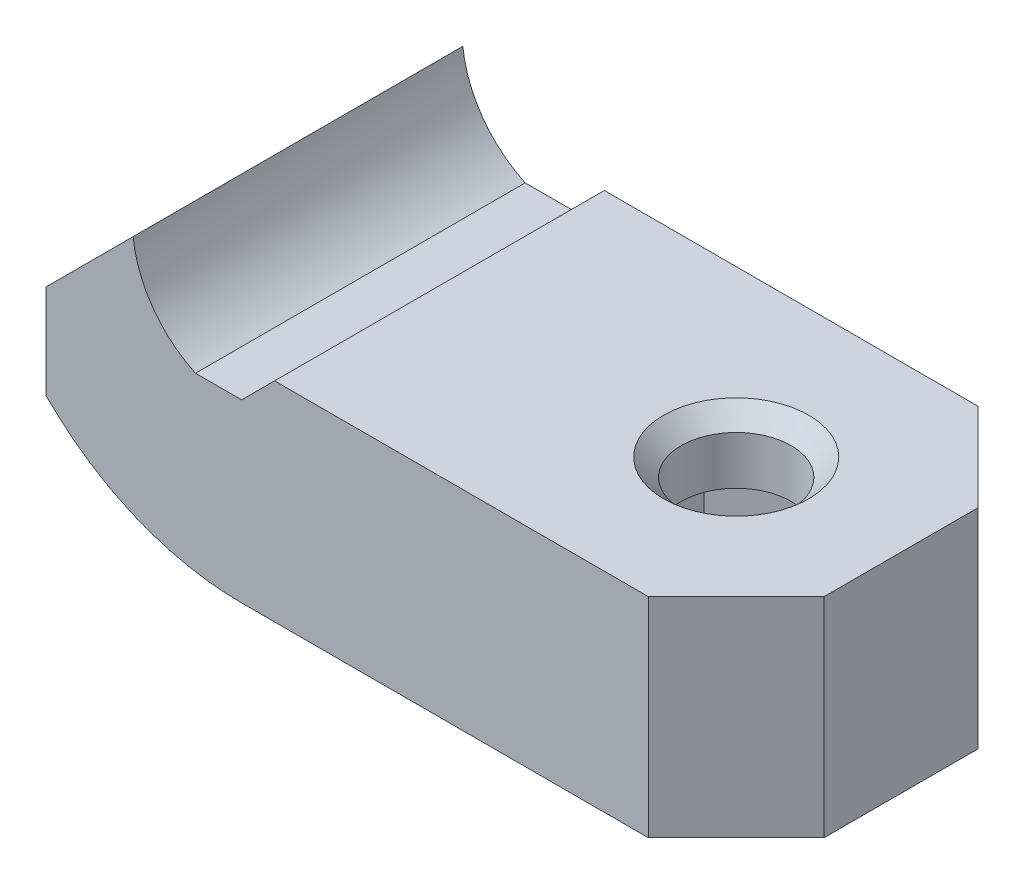
SolidWorks part; units mm, degrees
ref_plane "Alzado" through (0, 0, 0) normal (0, 0, 1) x (1, 0, 0)
ref_plane "Planta" through (0, 0, 0) normal (0, 1, 0) x (1, 0, 0)
ref_plane "Vista lateral" through (0, 0, 0) normal (1, 0, 0) x (0, 0, -1)
sketch "Croquis1" plane through (0, 0, 0) normal (0, 0, 1) x (1, 0, 0)
  line L0 (0, 0) -> (0, 5301.9663) construction
  line L1 (0, 0) -> (5301.9663, 0) construction
  line L2 (-4.8553, 4) -> (5297.111, 4) construction
  line L3 (0, 4) -> (-2.1, 4) construction
  line L4 (-8.9, 5.9678) -> (-8.9, -5295.9985) construction
  line L5 (-2.1, 7.8714) -> (-2.1, -5294.095) construction
  line L6 (-2.1, 4) -> (-2.1, 8.4) construction
  line L8 (-8.9, 4) -> (-8.9, -4) construction
  line L10 (-2.1, -4) -> (-2.1, -8.4) construction
  line L11 (0, -4) -> (-2.1, -4) construction
  line L12 (0, 4) -> (0, -4) construction
  line L13 (-4.5, -15.5102) -> (-4.5, 49984.4898) construction
  line L14 (-2.1, -8.4) -> (-4.5, -8.4) construction
  line L15 (-4.5, -8.4) -> (-8.9, -4) construction
  line L16 (-4.5, 8.4) -> (-8.9, 4) construction
  line L17 (-2.1, 8.4) -> (-4.5, 8.4) construction
  line L18 (17.5111, 5.5) -> (-49982.4889, 5.5) construction
  line L19 (23.2911, 8.5) -> (-49976.7089, 8.5) construction
  line L20 (-8.9, 4) -> (-4.9368, 7.9632)
  line L22 (-8.9, 4) -> (-8.9, -0.2772)
  line L23 (-2.1, 4) -> (0, 4)
  line L24 (0, 4) -> (0, -4)
  circle A0 centre (0, 8.5) radius 4.9659 construction
  circle A1 centre (0, 8.5) radius 12.5 construction
  arc A4 (0, -4) -> (-8.9, -0.2772) centre (0, 8.5) cw
  arc A5 (-2.1, 4) -> (-4.9368, 7.9632) centre (0, 8.5) cw
  point P17 (-8.9, 0)
  dimension "D1" = 8
  dimension "D2" = 6.8
  dimension "D3" = 2.1
  dimension "D4" = 8
  dimension "D5" = 16.8
  dimension "D6" = 2.4
  dimension "D7" = 1.5
  dimension "D8" = 3
extrude "Saliente-Extruir1" add sketch "Croquis1" along normal mid plane 15
sketch "Croquis6" plane through (0, 0, -7.5) normal (0, 0, -1) x (-1, 0, 0)
  line L0 (0, 0) -> (-50000, 0) construction
  line L1 (0, 0) -> (0, 50000) construction
  line L2 (-15, 0) -> (-15, 50000) construction
  line L3 (-3.8361, 5.5) -> (-50003.8361, 5.5) construction
  line L5 (0, 4) -> (-1.5, 5.5)
  line L6 (-1.5, 5.5) -> (-22.5, 5.5)
  line L7 (-22.5, 5.5) -> (-22.5, -4)
  line L8 (-22.5, -4) -> (0, -4)
  line L9 (0, -4) -> (0, 4)
  line L10 (0, 4) -> (2.1, 4) construction
  arc A0 (0, -4) -> (8.9, -0.2772) centre (0, 8.5) ccw construction
  point P14 (0, 4)
  point P19 (0, 4)
  point P21 (0, 0)
  point P22 (0, 0)
  point P23 (0, 0)
  point P24 (0, 0)
  point P25 (0, 0)
  point P26 (0, -4)
  point P30 (0, 0)
  point P31 (-22.5, -4)
  dimension "D1" = 15
  dimension "D2" = 1.5
  dimension "D3" = 15
  dimension "D4" = 45
extrude "Saliente-Extruir2" add sketch "Croquis6" against normal through all
sketch "Croquis7" plane through (0, 5.5, 0) normal (0, 1, 0) x (1, 0, 0)
  line L0 (0, 0) -> (50000, 0) construction
  line L1 (15, 0) -> (15, 50000) construction
  circle A0 centre (15, 0) radius 2.5
  dimension "D2" = 5
  dimension "D1" = 15
extrude "Cortar-Extruir4" cut sketch "Croquis7" against normal through all
sketch "Croquis8" plane through (0, 5.5, 0) normal (0, 1, 0) x (1, 0, 0)
  line L1 (15, 3.9837) -> (11.55, 1.9919)
  line L2 (11.55, 1.9919) -> (11.55, -1.9919)
  line L3 (11.55, -1.9919) -> (15, -3.9837)
  line L4 (15, -3.9837) -> (18.45, -1.9919)
  line L5 (18.45, -1.9919) -> (18.45, 1.9919)
  line L6 (18.45, 1.9919) -> (15, 3.9837)
  circle A0 centre (15, 0) radius 3.45 construction
  dimension "D1" = 6.9
extrude "Cortar-Extruir5" cut sketch "Croquis8" against normal blind 10 from offset 3 offset against normal yes
chamfer "Chaflán4" distance 4 angle 45 2 edges at (22.5, 0.75, -7.5) (22.5, 0.75, 7.5)
chamfer "Chaflán5" distance 0.8 angle 45 7 edges at (11.55, -4, 0) (13.275, -4, 2.9878) (16.725, -4, 2.9878) (18.45, -4, 0) (16.725, -4, -2.9878) (13.275, -4, -2.9878) (12.5, 5.5, 0)
